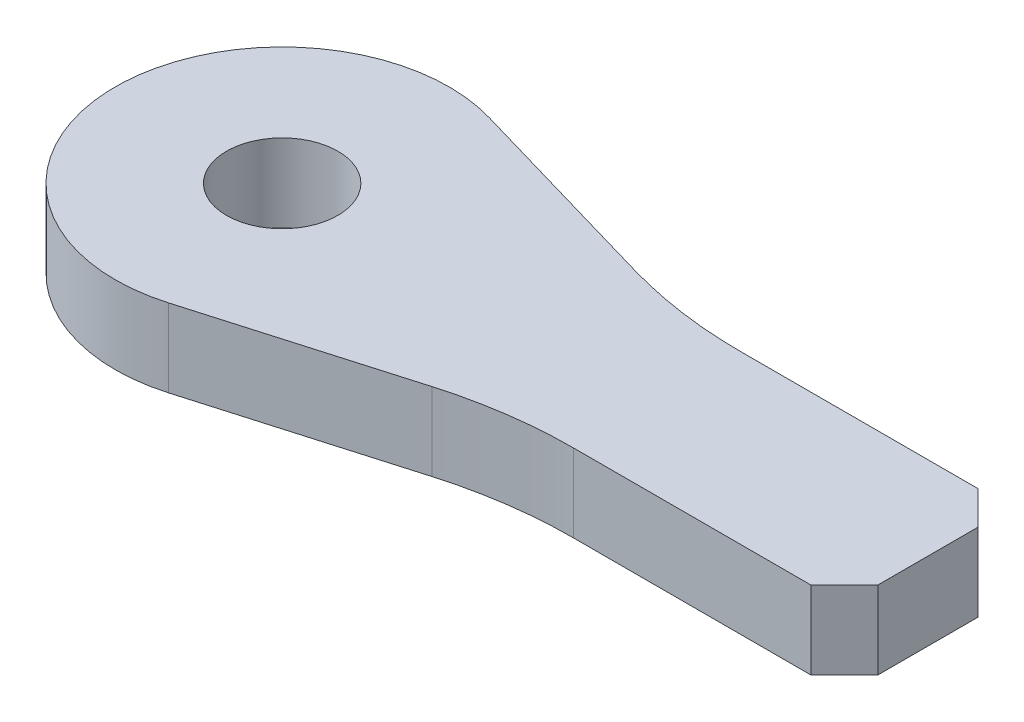
SolidWorks part; units mm, degrees
ref_plane "Front Plane" through (0, 0, 0) normal (0, 0, 1) x (1, 0, 0)
ref_plane "Top Plane" through (0, 0, 0) normal (0, 1, 0) x (1, 0, 0)
ref_plane "Right Plane" through (0, 0, 0) normal (1, 0, 0) x (0, 0, -1)
sketch "Sketch1" plane through (0, 0, 0) normal (0, 1, 0) x (1, 0, 0)
  line L8 (37.5, -4.5) -> (37.5, 4.5)
  line L9 (37.5, 4.5) -> (34.5, 7.5)
  line L10 (34.5, 7.5) -> (13.1837, 7.5)
  line L12 (13.1837, -7.5) -> (34.5, -7.5)
  line L13 (34.5, -7.5) -> (37.5, -4.5)
  line L15 (2.0413, 9.0832) -> (-16.3116, 14.4063)
  line L17 (2.0413, -9.0832) -> (-16.3116, -14.4063)
  arc A0 (-16.3116, 14.4063) -> (-16.3116, -14.4063) centre (-20.49, 0) ccw
  circle A5 centre (-20.49, 0) radius 5
  arc A7 (13.1837, -7.5) -> (2.0413, -9.0832) centre (13.1837, -47.5) ccw
  arc A8 (13.1837, 7.5) -> (2.0413, 9.0832) centre (13.1837, 47.5) cw
  dimension "D1" = 40
extrude "Boss-Extrude1" add sketch "Sketch1" along normal blind 7
